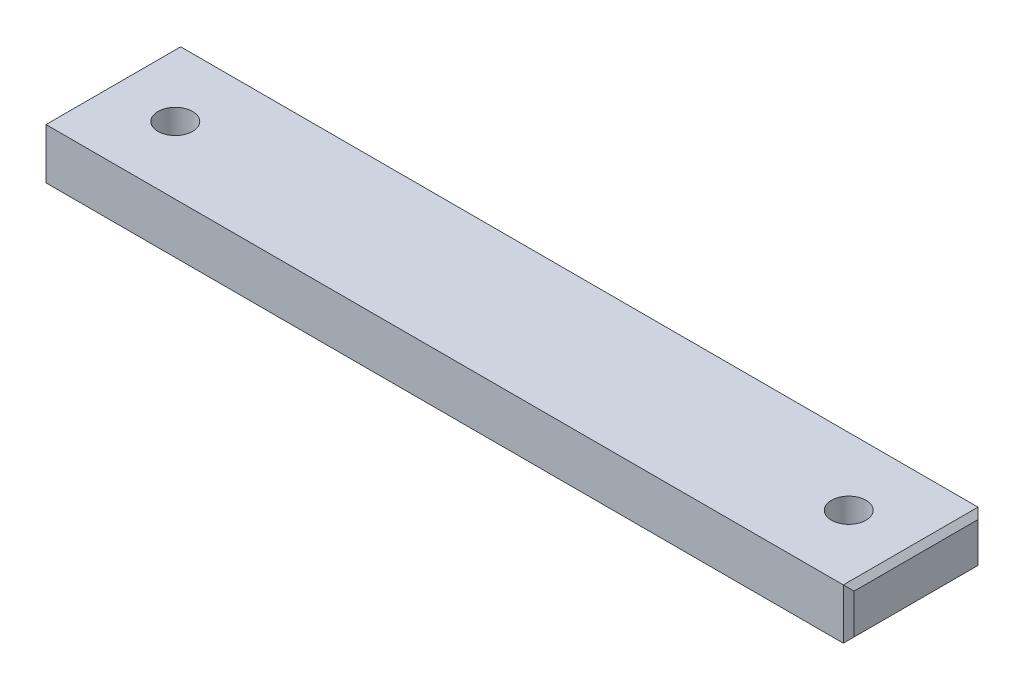
SolidWorks part; units mm, degrees
material "6061-T6 (SS)"
ref_plane "Front Plane" through (0, 0, 0) normal (0, 0, 1) x (1, 0, 0)
ref_plane "Top Plane" through (0, 0, 0) normal (0, 1, 0) x (1, 0, 0)
ref_plane "Right Plane" through (0, 0, 0) normal (1, 0, 0) x (0, 0, -1)
sketch "Sketch1" plane through (0, 0, 0) normal (0, 1, 0) x (1, 0, 0)
  line L0 (-63.5, 0) -> (0, 0) construction
  line L1 (-63.5, 6.35) -> (0, 6.35)
  line L2 (-63.5, -6.35) -> (0, -6.35)
  line L4 (6.35, -6.35) -> (-69.85, -6.35)
  line L5 (6.35, -6.35) -> (6.35, 6.35)
  line L6 (6.35, 6.35) -> (-69.85, 6.35)
  line L7 (-69.85, -6.35) -> (-69.85, 6.35)
  arc A0 (-63.5, 6.35) -> (-63.5, -6.35) centre (-63.5, 0) ccw
  arc A1 (0, -6.35) -> (0, 6.35) centre (0, 0) ccw
  point P2 (-31.75, 0)
  point P9 (-69.85, 0)
  point P10 (6.35, 0)
  dimension "D2" = 76.2
  dimension "D1" = 12.7
extrude "Boss-Extrude2" add sketch "Sketch1" along normal blind 4.7625
hole_wizard "#4 Clearance Hole1" positions "Sketch2" profile "Sketch4" hole size "#4" standard "ANSI Inch" end condition through all
sketch "Sketch2" plane through (0, 4.7625, 0) normal (0, 1, 0) x (1, 0, 0)
  point P3 (-63.5, 0)
  point P9 (0, 0)
sketch "Sketch4" plane through (-63.5, 4.7625, 0) normal (1, 0, 0) x (0, 0, 1)
  line L0 (0, 0) -> (0, 4.7625)
  line L1 (0, 4.7625) -> (1.6319, 4.7625)
  line L2 (1.6319, 4.7625) -> (1.6319, 0)
  line L5 (1.6319, 0) -> (0, 0)
  line L11 (0, -6.35) -> (0, 107.95) construction
  dimension "Thru Hole Dia." = 3.2639
  dimension "Thru Hole Depth" = 4.7625
hole_wizard "CSK for #4 Flat Head Socket Cap Screw2" positions "Sketch8" profile "Sketch9" countersink size "#4" standard "ANSI Inch" end condition through all
sketch "Sketch8" plane through (0, 0, 0) normal (0, -1, 0) x (-1, 0, 0)
  point P0 (0, 0)
sketch "Sketch9" plane through (0, 0, 0) normal (1, 0, 0) x (0, 0, -1)
  line L0 (0, 0) -> (0, 4.7625)
  line L1 (0, 4.7625) -> (1.6319, 4.7625)
  line L2 (1.6319, 4.7625) -> (1.6319, 1.8481)
  line L3 (1.6319, 1.8481) -> (3.2385, 0)
  line L5 (3.2385, 0) -> (0, 0)
  line L6 (-1.6319, 1.8481) -> (-3.2385, 0) construction
  line L11 (0, -6.35) -> (0, 107.95) construction
  dimension "Thru Hole Dia." = 3.2639
  dimension "Thru Hole Depth" = 4.7625
  dimension "Near C'Sink Dia." = 6.477
  dimension "Near C'Sink Angle" = 82
chamfer "Chamfer1" distance 0.508 angle 45 8 edges at (-69.85, 2.3813, -6.35) (-69.85, 0, 0) (-69.85, 4.7625, 0) (-69.85, 2.3813, 6.35) (6.35, 2.3813, 6.35) (6.35, 0, 0) (6.35, 4.7625, 0) (6.35, 2.3813, -6.35)
